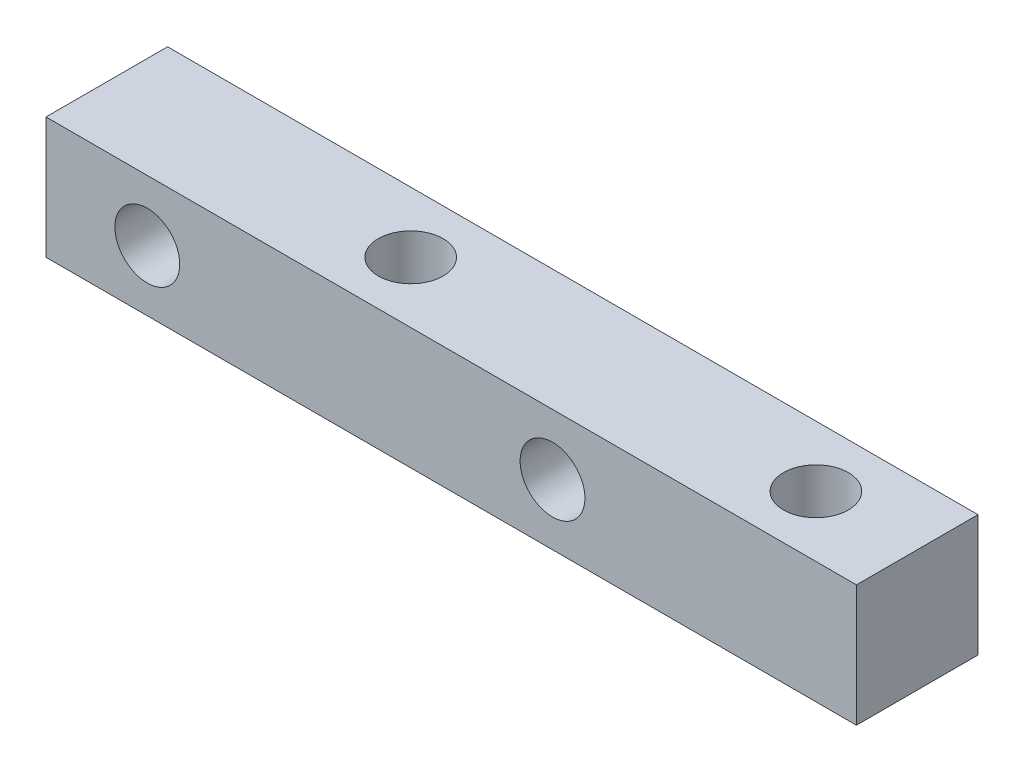
SolidWorks part; units mm, degrees
ref_plane "前视基准面" through (0, 0, 0) normal (0, 0, 1) x (1, 0, 0)
ref_plane "上视基准面" through (0, 0, 0) normal (0, 1, 0) x (1, 0, 0)
ref_plane "右视基准面" through (0, 0, 0) normal (1, 0, 0) x (0, 0, -1)
sketch "草图1" plane through (0, 0, 0) normal (0, 0, 1) x (1, 0, 0)
  line L0 (0, 0) -> (0, 6)
  line L1 (0, 6) -> (40, 6)
  line L2 (40, 6) -> (40, 0)
  line L3 (40, 0) -> (0, 0)
  circle A0 centre (5, 3) radius 1.6
  circle A1 centre (25, 3) radius 1.6
extrude "凸台-拉伸1" add sketch "草图1" along normal blind 6
sketch "草图2" plane through (0, 6, 0) normal (0, 1, 0) x (1, 0, 0)
  circle A0 centre (35, -3) radius 1.6
  circle A1 centre (15, -3) radius 1.6
extrude "切除-拉伸1" cut sketch "草图2" against normal blind 6
